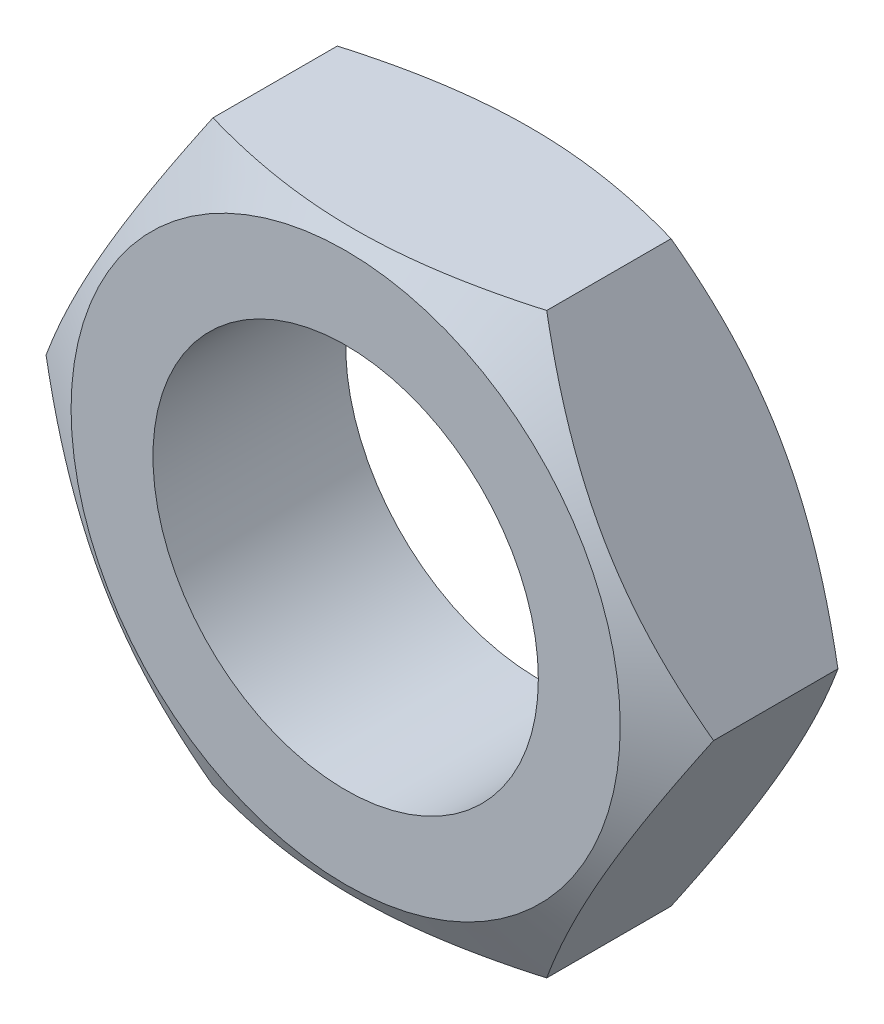
SolidWorks part; units mm, degrees
ref_plane "Plane1" through (0, 0, 0) normal (0, 0, 1) x (1, 0, 0)
ref_plane "Plane2" through (0, 0, 0) normal (0, 1, 0) x (1, 0, 0)
ref_plane "Plane3" through (0, 0, 0) normal (1, 0, 0) x (0, 0, -1)
sketch "BaseNutSke" plane through (0, 0, 0) normal (0, 0, 1) x (1, 0, 0)
  line L6 (8.6603, -15) -> (-8.6603, -15)
  line L7 (8.6603, 15) -> (-8.6603, 15)
  line L8 (8.6603, -15) -> (17.3205, 0)
  line L9 (17.3205, 0) -> (8.6603, 15)
  line L10 (-8.6603, 15) -> (-17.3205, 0)
  line L11 (-17.3205, 0) -> (-8.6603, -15)
  circle A0 centre (0, 0) radius 8.75 construction
  circle A1 centre (0, 0) radius 17.3205 construction
  circle A2 centre (0, 0) radius 10
  dimension "Tap_drill" = 17.5
  dimension "Diameter" = 20
  dimension "Width_flats" = 30
extrude "BaseNut" add sketch "BaseNutSke" against normal blind 10
cosmetic thread "ThreadCosmetic" [suppressed] parameters "Thread_major"=20
ref_plane "Plane4" through (0, 0, -5) normal (0, 0, -1) x (-1, 0, 0)
sketch "Sketch6" plane through (0, 0, -10) normal (0, 0, -1) x (-1, 0, 0)
  circle A0 centre (0, 0) radius 14.25
  dimension "D1" = 28.5
extrude "Cut-Extrude2" cut sketch "Sketch6" against normal through all draft 60 flip side to cut
mirror "Mirror1" about plane through (0, 0, -5) normal (0, 0, -1) of "Cut-Extrude2"
equation "\"D1@Sketch3\" = \"Width_flats@BaseNutSke\" /2"
equation "' \"Num_threads@ThdSchPat\" = \"Num_threads@ThdSchPat\" - sgn( \"Num_threads@ThdSchPat\" - 1) '---chamfered tips only---"
equation "\"D1@Sketch6\" = 0.95 * \"Width_flats@BaseNutSke\""
